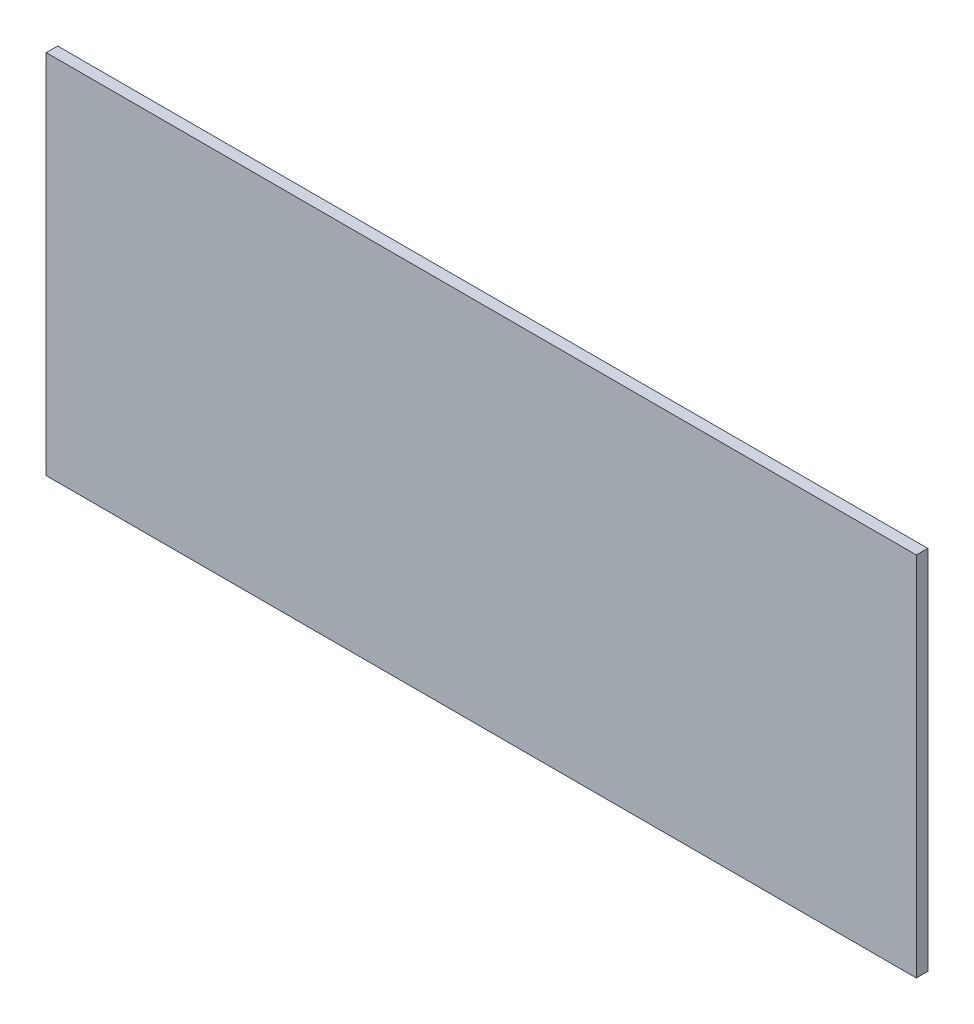
SolidWorks part; units mm, degrees
ref_plane "Front Plane" through (0, 0, 0) normal (0, 0, 1) x (1, 0, 0)
ref_plane "Top Plane" through (0, 0, 0) normal (0, 1, 0) x (1, 0, 0)
ref_plane "Right Plane" through (0, 0, 0) normal (1, 0, 0) x (0, 0, -1)
sketch "Sketch1" plane through (0, 0, 0) normal (0, 0, 1) x (1, 0, 0)
  line L0 (0, 0) -> (120.65, 0)
  line L1 (0, 0) -> (0, 50.8)
  line L2 (120.65, 0) -> (120.65, 50.8)
  line L3 (0, 50.8) -> (120.65, 50.8)
  dimension "D1" = 50.8
  dimension "D2" = 120.65
extrude "Boss-Extrude1" add sketch "Sketch1" along normal blind 1.5875
